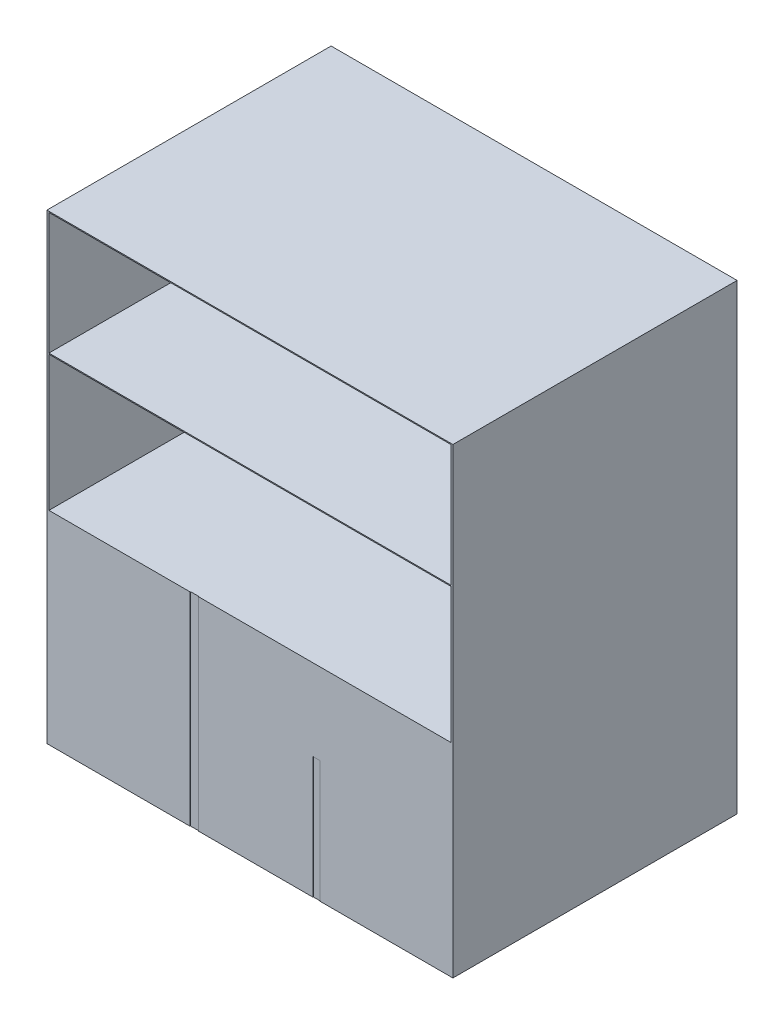
SolidWorks part; units mm, degrees
ref_plane "Alzado" through (0, 0, 0) normal (0, 0, 1) x (1, 0, 0)
ref_plane "Planta" through (0, 0, 0) normal (0, 1, 0) x (1, 0, 0)
ref_plane "Vista lateral" through (0, 0, 0) normal (1, 0, 0) x (0, 0, -1)
sketch "Croquis1" plane through (0, 0, 0) normal (0, 1, 0) x (1, 0, 0)
  line L1 (-1000, 700) -> (1000, 700)
  line L2 (-1000, 700) -> (-1000, -700)
  line L3 (-1000, -700) -> (1000, -700)
  line L4 (1000, 700) -> (1000, -700)
  line L5 (-1000, 700) -> (1000, -700) construction
  line L6 (-1000, -700) -> (1000, 700) construction
  point P0 (0, 0)
  dimension "D1" = 2000
  dimension "D2" = 1400
extrude "Saliente-Extruir1" add sketch "Croquis1" along normal blind 1000
sketch "Croquis2" plane through (0, 0, 700) normal (0, 0, 1) x (1, 0, 0)
  line L0 (-1000, 0) -> (1000, 0) construction
  line L2 (-294.6483, 1000) -> (-253.9268, 1000)
  line L4 (-294.6483, 1000) -> (-294.6483, 0)
  line L5 (-294.6483, 0) -> (-253.9268, 0)
  line L6 (-253.9268, 1000) -> (-253.9268, 0)
  line L7 (-294.6483, 1000) -> (-253.9268, 0) construction
  line L8 (-294.6483, 0) -> (-253.9268, 1000) construction
  line L9 (-1000, 1000) -> (1000, 1000) construction
  line L11 (310.3007, 600) -> (344.9141, 600)
  line L12 (310.3007, 600) -> (310.3007, 0)
  line L13 (310.3007, 0) -> (344.9141, 0)
  line L14 (344.9141, 600) -> (344.9141, 0)
  line L15 (310.3007, 600) -> (344.9141, 0) construction
  line L16 (310.3007, 0) -> (344.9141, 600) construction
  point P0 (-274.2876, 500)
  point P8 (327.6074, 300)
extrude "Cortar-Extruir1" cut sketch "Croquis2" against normal blind 2
sketch "Croquis5" plane through (0, 1000, 0) normal (0, 1, 0) x (1, 0, 0)
  line L0 (1000, -700) -> (990, -700)
  line L1 (-1000, -700) -> (-1000, 700)
  line L2 (-1000, 700) -> (1000, 700)
  line L3 (1000, 700) -> (1000, -700)
  line L4 (990, 690) -> (990, -690)
  line L5 (-990, -690) -> (-990, -700)
  line L6 (-990, -690) -> (-990, 690)
  line L7 (-990, 690) -> (990, 690)
  line L9 (990, -690) -> (990, -700)
  line L10 (-990, -700) -> (-1000, -700)
  line L11 (990, -690) -> (-990, -690) construction
  line L12 (1000, -700) -> (-1000, -700) construction
  dimension "D1" = 10
extrude "Saliente-Extruir2" add sketch "Croquis5" along normal blind 666
sketch "Croquis6" plane through (0, 1666, 0) normal (0, 1, 0) x (1, 0, 0)
  line L0 (-1000, 700) -> (1000, 700)
  line L1 (1000, 700) -> (1000, -700)
  line L2 (1000, -700) -> (-1000, -700)
  line L3 (-1000, -700) -> (-1000, 700)
extrude "Saliente-Extruir3" add sketch "Croquis6" along normal blind 610
sketch "Croquis7" plane through (0, 0, 700) normal (0, 0, 1) x (1, 0, 0)
  line L0 (-990, 1666) -> (990, 1666) construction
  line L1 (-990, 2271) -> (990, 2271)
  line L2 (-990, 2271) -> (-990, 1671)
  line L3 (-990, 1671) -> (990, 1671)
  line L4 (990, 2271) -> (990, 1671)
  line L5 (-990, 2271) -> (990, 1671) construction
  line L6 (-990, 1671) -> (990, 2271) construction
  line L7 (-1000, 2276) -> (1000, 2276) construction
  line L8 (1000, 2276) -> (1000, 0) construction
  line L9 (-1000, 2276) -> (-1000, 0) construction
  point P0 (0, 1971)
  dimension "D1" = 5
  dimension "D2" = 5
  dimension "D3" = 10
  dimension "D4" = 10
extrude "Cortar-Extruir4" cut sketch "Croquis7" against normal blind 1300
